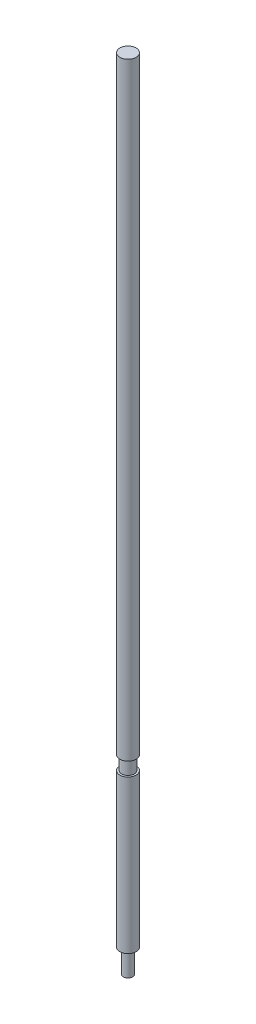
SolidWorks part; units mm, degrees
ref_plane "Alzado" through (0, 0, 0) normal (0, 0, 1) x (1, 0, 0)
ref_plane "Planta" through (0, 0, 0) normal (0, 1, 0) x (1, 0, 0)
ref_plane "Vista lateral" through (0, 0, 0) normal (1, 0, 0) x (0, 0, -1)
sketch "Croquis1" plane through (0, 0, 0) normal (0, 0, 1) x (1, 0, 0)
  line L0 (0, 19.92) -> (0, -31.3029) construction
  line L1 (0, 290.4013) -> (-4.14, 290.4013)
  line L2 (-4.14, 290.4013) -> (-4.14, -19.5987)
  line L3 (-4.14, -19.5987) -> (-3.185, -19.5987)
  line L4 (-3.185, -19.5987) -> (-3.185, -26.5987)
  line L5 (-3.185, -26.5987) -> (-4.14, -26.5987)
  line L6 (-4.14, -26.5987) -> (-4.14, -104.5987)
  line L7 (-4.14, -104.5987) -> (-2.385, -104.5987)
  line L8 (-2.385, -104.5987) -> (-2.385, -116.5987)
  line L9 (-2.385, -116.5987) -> (0, -116.5987)
  line L10 (0, -116.5987) -> (0, 290.4013)
  dimension "D1" = 8.28
  dimension "D2" = 6.37
  dimension "D3" = 4.77
  dimension "D4" = 12
  dimension "D5" = 78
  dimension "D6" = 7
  dimension "D7" = 310
revolve "Revolución1" add sketch "Croquis1" angle 360 about L0
